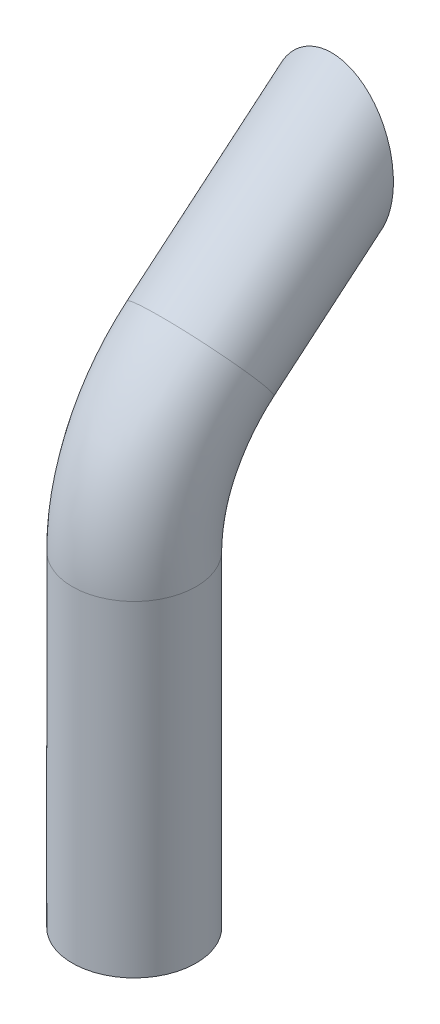
SolidWorks part; units mm, degrees
ref_plane "Front Plane" through (0, 0, 0) normal (0, 0, 1) x (1, 0, 0)
ref_plane "Top Plane" through (0, 0, 0) normal (0, 1, 0) x (1, 0, 0)
ref_plane "Right Plane" through (0, 0, 0) normal (1, 0, 0) x (0, 0, -1)
sketch "Sketch1" plane through (0, 0, 0) normal (1, 0, 0) x (0, 0, -1)
  line L0 (0, 0) -> (-82.7576, -69.4418)
  line L1 (-114.9067, -138.3858) -> (-114.9067, -296.4181)
  arc A0 (-82.7576, -69.4418) -> (-114.9067, -138.3858) centre (-24.9067, -138.3858) ccw
  point P3 (-150, -200)
  point P5 (-150, 0)
  point P6 (-129.3927, -75.8784)
  point P7 (-132.2454, -270.7895)
  point P10 (-114.9067, -96.4181)
  dimension "D4" = 90
  dimension "D1" = 150
  dimension "D2" = 200
  dimension "D3" = 130
ref_plane "Plane1" through (0, 0, 0) normal (0, -0.6428, 0.766) x (1, 0, 0)
sketch "Sketch2" plane through (0, 0, 0) normal (0, -0.6428, 0.766) x (1, 0, 0)
  circle A0 centre (0, 0) radius 30
  dimension "D1" = 60
sweep "Sweep-Thin1" add profiles "Sketch2" path "Sketch1" parameters "D1"=3
sketch "Sketch3" plane through (0, 0, 0) normal (1, 0, 0) x (0, 0, -1)
  line L1 (-19.2836, 22.9813) -> (55.3633, 22.9813)
  line L2 (-19.2836, 22.9813) -> (-19.2836, -79.5517)
  line L3 (-19.2836, -79.5517) -> (55.3633, -79.5517)
  line L4 (55.3633, 22.9813) -> (55.3633, -79.5517)
extrude "Cut-Extrude1" cut sketch "Sketch3" against normal mid plane 130
